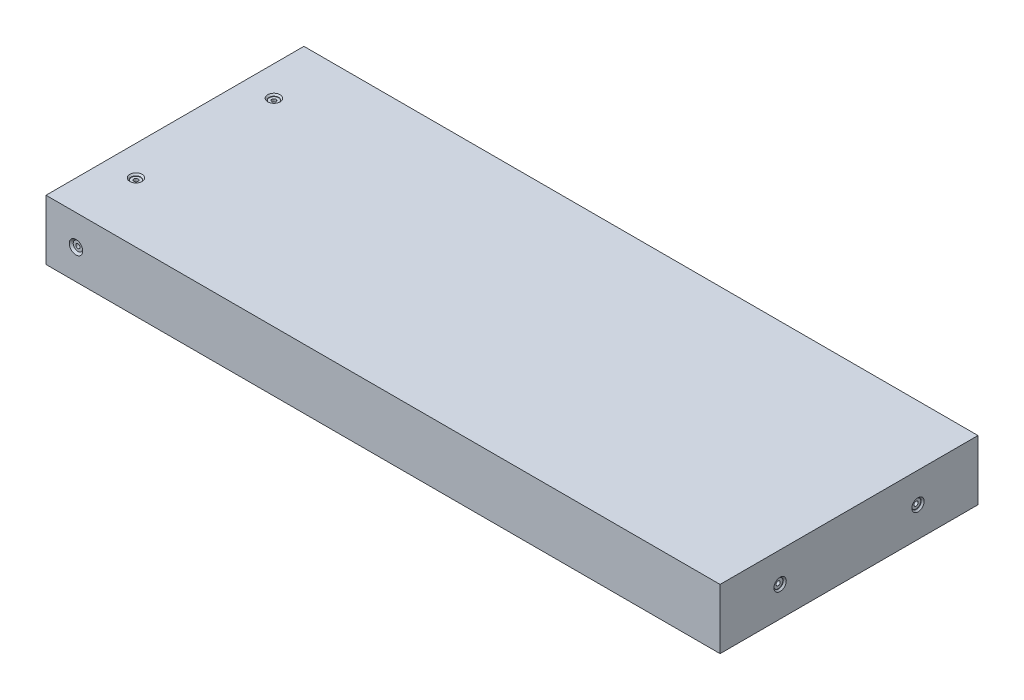
SolidWorks part; units mm, degrees
material "Balsa"
ref_plane "Front Plane" through (0, 0, 0) normal (0, 0, 1) x (1, 0, 0)
ref_plane "Top Plane" through (0, 0, 0) normal (0, 1, 0) x (1, 0, 0)
ref_plane "Right Plane" through (0, 0, 0) normal (1, 0, 0) x (0, 0, -1)
sketch "Sketch1" plane through (0, 0, 0) normal (0, 1, 0) x (1, 0, 0)
  line L1 (-142.7, 54.6) -> (142.7, 54.6)
  line L2 (-142.7, 54.6) -> (-142.7, -54.6)
  line L3 (-142.7, -54.6) -> (142.7, -54.6)
  line L4 (142.7, 54.6) -> (142.7, -54.6)
  line L5 (-142.7, 54.6) -> (142.7, -54.6) construction
  line L6 (-142.7, -54.6) -> (142.7, 54.6) construction
  point P0 (0, 0)
  dimension "D1" = 109.2
  dimension "D2" = 285.4
extrude "Boss-Extrude1" add sketch "Sketch1" along normal blind 25.4
hole_wizard "CBORE for #0 Binding Head Machine Screw1" positions "Sketch2" profile "Sketch3" counterbore size "#0" standard "ANSI Inch"
sketch "Sketch2" plane through (0, 0, 54.6) normal (0, 0, 1) x (1, 0, 0)
  line L0 (-142.7, 25.4) -> (-142.7, 0) construction
  line L1 (-142.7, 25.4) -> (142.7, 25.4) construction
  point P0 (-130, 12.7)
  dimension "D1" = 12.7
  dimension "D2" = 12.7
sketch "Sketch3" plane through (-130, 12.7, 54.6) normal (1, 0, 0) x (0, -1, 0)
  line L0 (0, 0) -> (0, 30.5342)
  line L1 (0, 30.5342) -> (0.889, 30)
  line L2 (0.889, 30) -> (0.889, 0.8128)
  line L3 (0.889, 0.8128) -> (1.985, 0.8128)
  line L5 (1.985, 0.8128) -> (1.985, 0.8725)
  line L6 (1.985, 0.8725) -> (2.8575, 0)
  line L7 (2.8575, 0) -> (0, 0)
  line L8 (-1.985, 0.8725) -> (-2.8575, 0) construction
  line L10 (0, 30.5342) -> (-0.889, 30) construction
  line L11 (0, -6.35) -> (0, 107.95) construction
  dimension "Hole Dia." = 1.778
  dimension "Hole Depth" = 30
  dimension "C'Bore Dia." = 3.97
  dimension "C'Bore Depth" = 0.8128
  dimension "Near C'Sink Dia." = 5.715
  dimension "Near C'Sink Angle" = 90
  dimension "Drill Angle" = 118
mirror "Mirror1" about plane through (0, 0, 0) normal (0, 0, 1) of "CBORE for #0 Binding Head Machine Screw1"
hole_wizard "CBORE for #0 Binding Head Machine Screw2" positions "Sketch4" profile "Sketch5" counterbore size "#0" standard "ANSI Inch"
sketch "Sketch4" plane through (142.7, 0, 0) normal (1, 0, 0) x (0, 0, -1)
  line L0 (-54.6, 25.4) -> (-54.6, 0) construction
  line L2 (-54.6, 25.4) -> (54.6, 25.4) construction
  point P0 (-30, -45.7)
  point P2 (-29.1995, 12.7)
  dimension "D1" = 25.4005
  dimension "D2" = 24.6
  dimension "D4" = 12.7
sketch "Sketch5" plane through (142.7, -45.7, 30) normal (0, 1, 0) x (0, 0, -1)
  line L0 (0, 0) -> (0, 30.5342)
  line L1 (0, 30.5342) -> (0.889, 30)
  line L2 (0.889, 30) -> (0.889, 0.8128)
  line L3 (0.889, 0.8128) -> (1.985, 0.8128)
  line L5 (1.985, 0.8128) -> (1.985, 0.635)
  line L6 (1.985, 0.635) -> (2.62, 0)
  line L7 (2.62, 0) -> (0, 0)
  line L8 (-1.985, 0.635) -> (-2.62, 0) construction
  line L10 (0, 30.5342) -> (-0.889, 30) construction
  line L11 (0, -6.35) -> (0, 107.95) construction
  dimension "Hole Dia." = 1.778
  dimension "Hole Depth" = 30
  dimension "C'Bore Dia." = 3.97
  dimension "C'Bore Depth" = 0.8128
  dimension "Near C'Sink Dia." = 5.24
  dimension "Near C'Sink Angle" = 90
  dimension "Drill Angle" = 118
hole_wizard "CBORE for #0 Binding Head Machine Screw3" positions "Sketch6" profile "Sketch7" counterbore size "#0" standard "ANSI Inch"
sketch "Sketch6" plane through (0, 25.4, 0) normal (0, 1, 0) x (1, 0, 0)
  line L0 (-142.7, 54.6) -> (-142.7, -54.6) construction
  line L1 (142.7, 54.6) -> (-142.7, 54.6) construction
  point P0 (-130, 29.1995)
  point P2 (-130, -29.2005)
  dimension "D1" = 12.7
  dimension "D2" = 58.4
  dimension "D3" = 25.4005
  dimension "D4" = 12.7
sketch "Sketch7" plane through (-130, 25.4, -29.1995) normal (1, 0, 0) x (0, 0, 1)
  line L0 (0, 0) -> (0, 30.5342)
  line L1 (0, 30.5342) -> (0.889, 30)
  line L2 (0.889, 30) -> (0.889, 0.8128)
  line L3 (0.889, 0.8128) -> (1.985, 0.8128)
  line L5 (1.985, 0.8128) -> (1.985, 0.635)
  line L6 (1.985, 0.635) -> (2.62, 0)
  line L7 (2.62, 0) -> (0, 0)
  line L8 (-1.985, 0.635) -> (-2.62, 0) construction
  line L10 (0, 30.5342) -> (-0.889, 30) construction
  line L11 (0, -6.35) -> (0, 107.95) construction
  dimension "Hole Dia." = 1.778
  dimension "Hole Depth" = 30
  dimension "C'Bore Dia." = 3.97
  dimension "C'Bore Depth" = 0.8128
  dimension "Near C'Sink Dia." = 5.24
  dimension "Near C'Sink Angle" = 90
  dimension "Drill Angle" = 118
pattern_linear "LPattern1" count 2 spacing 58.4 along (0, 0, -1) of "CBORE for #0 Binding Head Machine Screw2"
